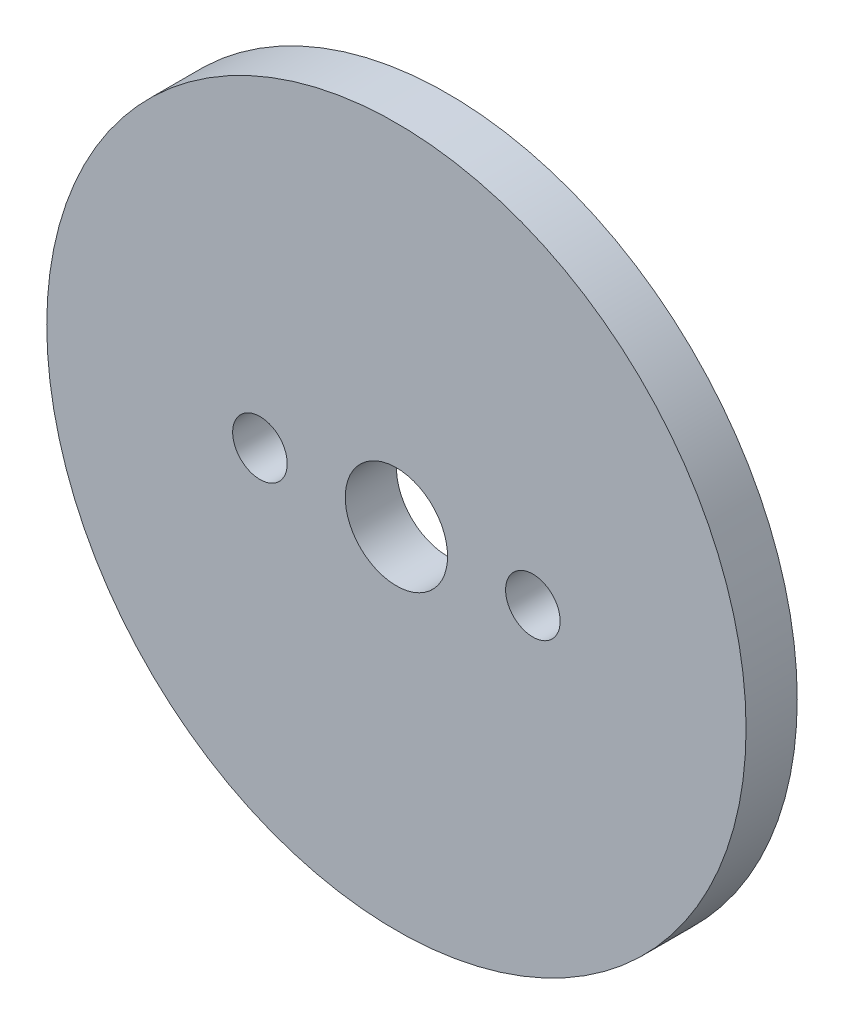
SolidWorks part; units mm, degrees
material "MDF"
ref_plane "Plano frontal" through (0, 0, 0) normal (0, 0, 1) x (1, 0, 0)
ref_plane "Plano superior" through (0, 0, 0) normal (0, 1, 0) x (1, 0, 0)
ref_plane "Plano direito" through (0, 0, 0) normal (1, 0, 0) x (0, 0, -1)
sketch "Esboço1" plane through (0, 0, 0) normal (0, 0, 1) x (1, 0, 0)
  line L0 (-8, 0) -> (8, 0) construction
  circle A0 centre (0, 0) radius 20.5
  circle A1 centre (0, 0) radius 3
  circle A2 centre (-8, 0) radius 1.6
  circle A3 centre (8, 0) radius 1.6
  dimension "D1" = 3.2
  dimension "D2" = 6
  dimension "D4" = 41
  dimension "D3" = 16
extrude "Ressalto-extrusão1" add sketch "Esboço1" along normal mid plane 3
